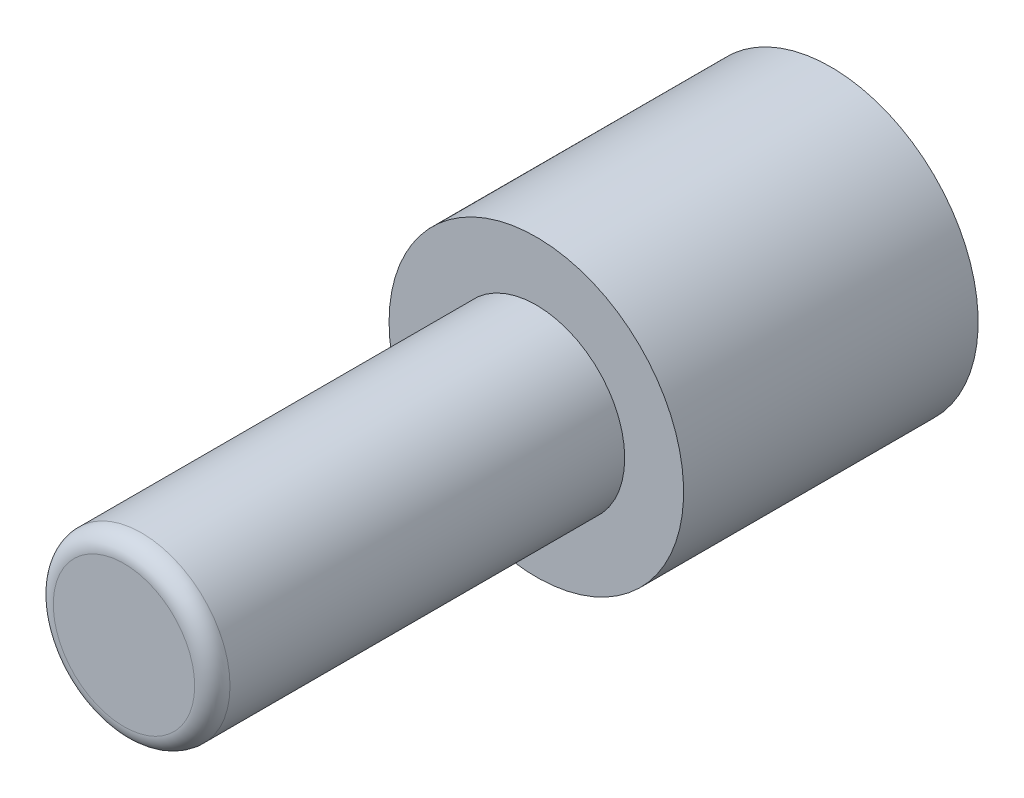
SolidWorks part; units mm, degrees
ref_plane "Front" through (0, 0, 0) normal (0, 0, 1) x (1, 0, 0)
ref_plane "Top" through (0, 0, 0) normal (0, 1, 0) x (1, 0, 0)
ref_plane "Right" through (0, 0, 0) normal (1, 0, 0) x (0, 0, -1)
sketch "Sketch1" plane through (0, 0, 0) normal (0, 0, 1) x (1, 0, 0)
  circle A0 centre (0, 0) radius 1.5
  dimension "D1" = 3
extrude "Boss-Extrude1" add sketch "Sketch1" along normal blind 7
sketch "Sketch2" plane through (0, 0, 0) normal (0, 0, -1) x (-1, 0, 0)
  circle A0 centre (0, 0) radius 2.5
  dimension "D1" = 5
extrude "Boss-Extrude2" add sketch "Sketch2" along normal blind 5
fillet "Fillet2" radius 0.3 1 edges at (1.5, 0, 7)
